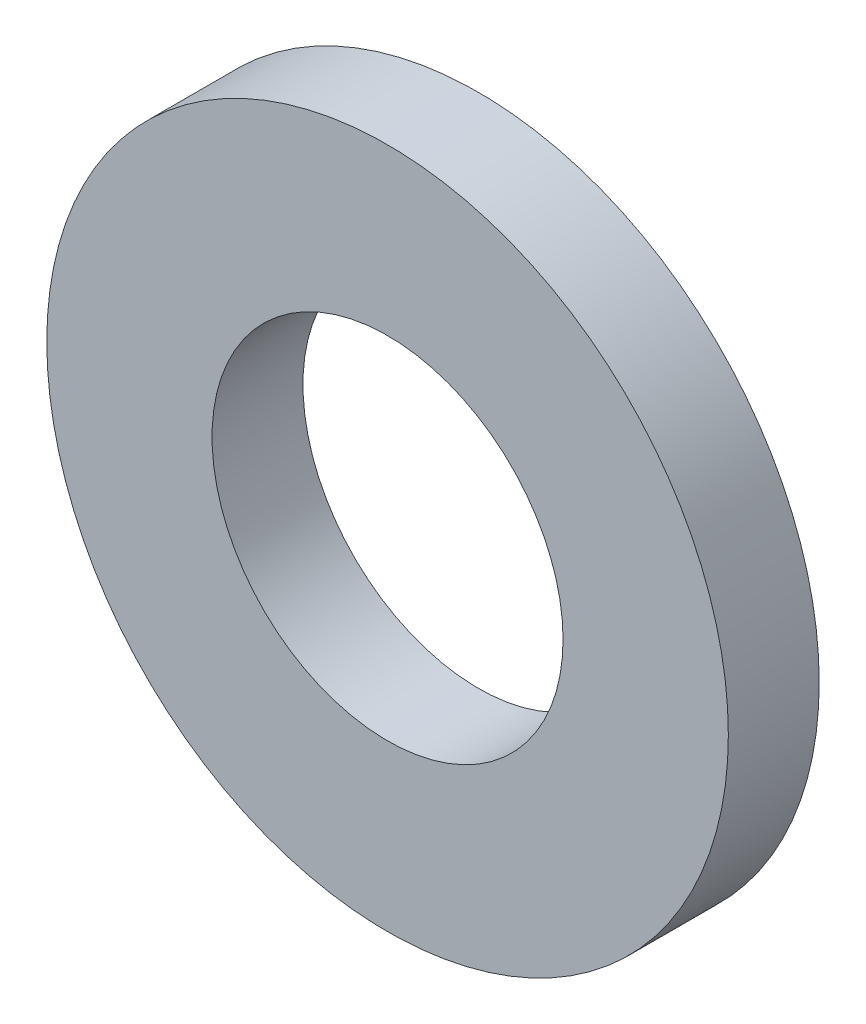
SolidWorks part; units mm, degrees
ref_plane "Front" through (0, 0, 0) normal (0, 0, 1) x (1, 0, 0)
ref_plane "Top" through (0, 0, 0) normal (0, 1, 0) x (1, 0, 0)
ref_plane "Right" through (0, 0, 0) normal (1, 0, 0) x (0, 0, -1)
sketch "Sketch1" plane through (0, 0, 0) normal (0, 0, 1) x (1, 0, 0)
  circle A0 centre (0, 0) radius 3.09
  circle A1 centre (0, 0) radius 6
  dimension "d1" = 6.18
  dimension "d2" = 12
extrude "Base-Extrude" add sketch "Sketch1" against normal blind 1.6
